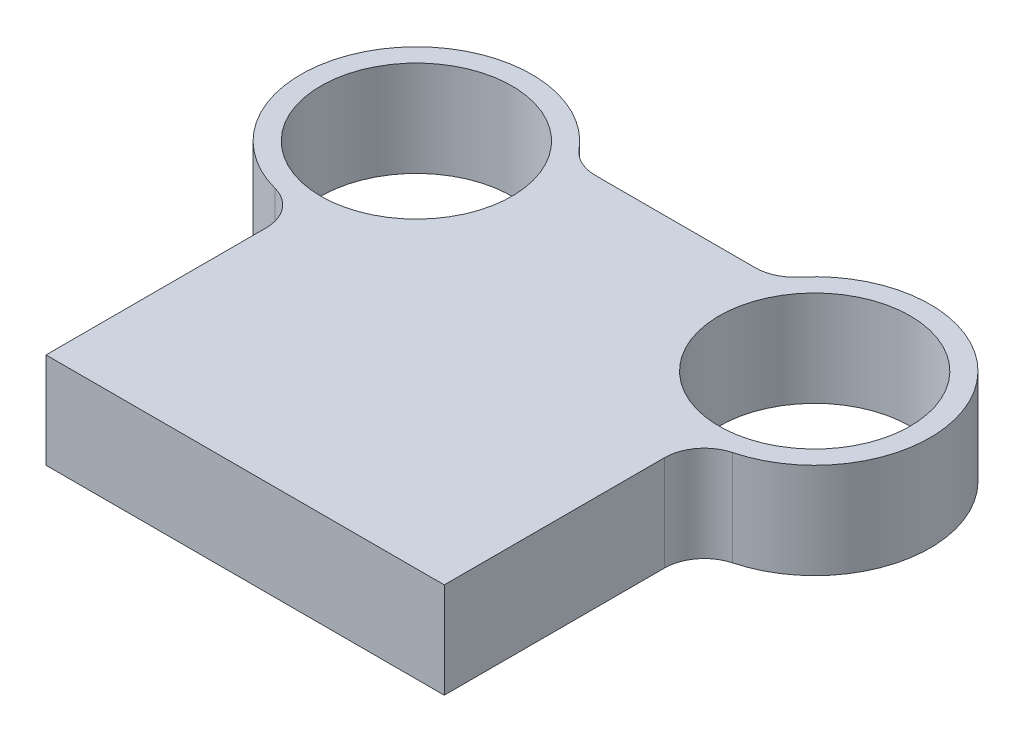
SolidWorks part; units mm, degrees
ref_plane "Front Plane" through (0, 0, 0) normal (0, 0, 1) x (1, 0, 0)
ref_plane "Top Plane" through (0, 0, 0) normal (0, 1, 0) x (1, 0, 0)
ref_plane "Right Plane" through (0, 0, 0) normal (1, 0, 0) x (0, 0, -1)
sketch "Sketch1" plane through (0, 0, 0) normal (0, 1, 0) x (1, 0, 0)
  line L0 (50, 0) -> (-50, 0)
  line L1 (-50, 0) -> (-50, 64)
  line L2 (0, 0) -> (0, 108) construction
  line L3 (25.1807, 108) -> (-25.1807, 108)
  line L4 (50, 0) -> (50, 64)
  arc A0 (-25.1807, 108) -> (-50, 64) centre (-50, 93) ccw
  circle A1 centre (-50, 93) radius 24
  arc A2 (25.1807, 108) -> (50, 64) centre (50, 93) cw
  circle A3 centre (50, 93) radius 24
  point P12 (-50, 32)
  point P18 (50, 32)
  dimension "D2" = 58
  dimension "D3" = 48
  dimension "D1" = 100
  dimension "D4" = 93
  dimension "D5" = 100
  dimension "D6" = 108
extrude "Boss-Extrude1" add sketch "Sketch1" along normal blind 24
fillet "Fillet1" radius 10 4 edges at (50, 12, -64) (25.1807, 12, -108) (-25.1807, 12, -108) (-50, 12, -64)
